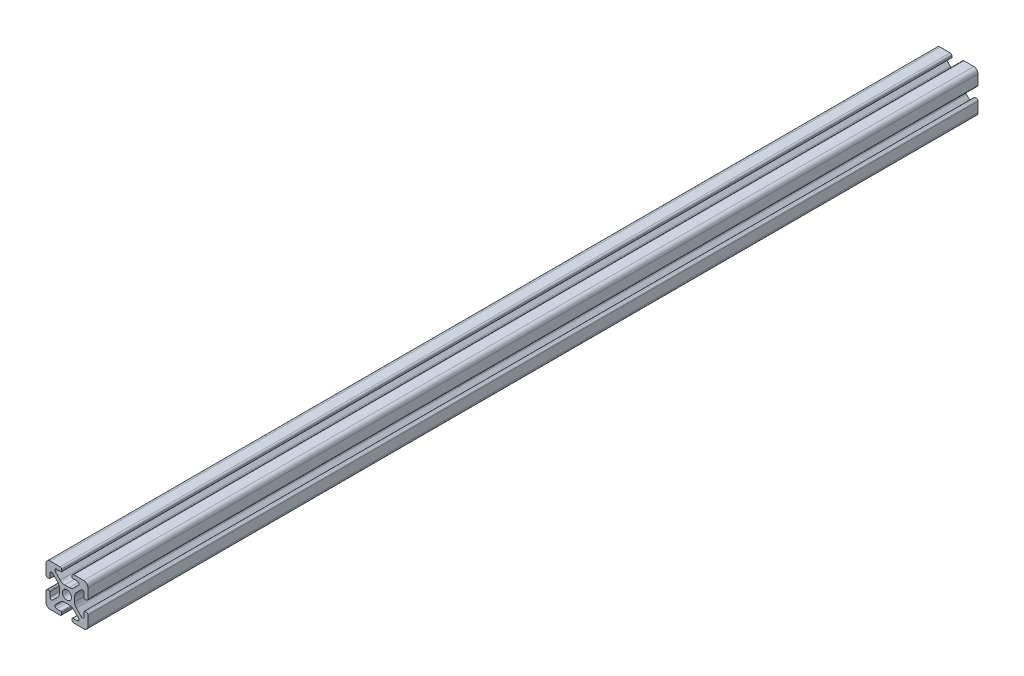
SolidWorks part; units mm, degrees
ref_plane "Front Plane" through (0, 0, 0) normal (0, 0, 1) x (1, 0, 0)
ref_plane "Top Plane" through (0, 0, 0) normal (0, 1, 0) x (1, 0, 0)
ref_plane "Right Plane" through (0, 0, 0) normal (1, 0, 0) x (0, 0, -1)
sketch "Sketch1" plane through (0, 0, 0) normal (0, 0, 1) x (1, 0, 0)
  line L0 (0, 10) -> (0, -10) construction
  line L1 (10, 0) -> (-10, 0) construction
  line L2 (-2.5, 10) -> (2.5, 10) construction
  line L3 (-5.75, 8.2) -> (5.75, 8.2) construction
  circle A0 centre (0, 0) radius 2.15 construction
  point P4 (0, 0)
  point P8 (0, 0)
  point P10 (0, 3.6)
  point P14 (0, 10)
  point P17 (0, 8.2)
  dimension "Thru Hole" = 4.3
  dimension "Height" = 20
  dimension "T Slot Depth" = 6.4
  dimension "T Slot Top Width" = 5
  dimension "T Slot Max Width" = 11.5
  dimension "Wall" = 1.8
sketch "Sketch2" plane through (0, 0, 0) normal (1, 0, 0) x (0, 0, -1)
  line L0 (212.5, 0) -> (-212.5, 0) construction
  point P4 (0, 0)
  dimension "D1" = 425
sketch "Sketch3" plane through (0, 0, 0) normal (0, 0, 1) x (1, 0, 0)
  line L0 (3.2874, 10) -> (8, 10)
  line L1 (10, 8) -> (10, -8) construction
  line L2 (8, -10) -> (-8, -10) construction
  line L3 (-10, 10) -> (10, -10) construction
  line L4 (2.5, 9.2126) -> (2.5, 8.5048)
  line L5 (-5.75, 8.2) -> (5.75, 8.2) construction
  line L6 (2.8048, 8.2) -> (4.9118, 8.2)
  line L7 (5.5045, 6.7691) -> (3.2141, 4.4787)
  line L8 (1.0928, 3.6) -> (-1.0928, 3.6)
  line L9 (0, 10) -> (0, -10) construction
  line L10 (5.75, 8.2) -> (5.75, 0) construction
  line L11 (10, 0) -> (-10, 0) construction
  line L12 (0, 0) -> (0, 10) construction
  line L13 (-2.5, 9.2126) -> (-2.5, 8.5048)
  line L14 (-5.5045, 6.7691) -> (-3.2141, 4.4787)
  line L15 (-2.8048, 8.2) -> (-4.9118, 8.2)
  line L16 (-3.2874, 10) -> (-8, 10)
  line L17 (0, 0) -> (-10, 0) construction
  line L18 (-10, 3.2874) -> (-10, 8)
  line L19 (-8.2, 2.8048) -> (-8.2, 4.9118)
  line L20 (-6.7691, 5.5045) -> (-4.4787, 3.2141)
  line L21 (-9.2126, 2.5) -> (-8.5048, 2.5)
  line L22 (-3.6, -1.0928) -> (-3.6, 1.0928)
  line L23 (-6.7691, -5.5045) -> (-4.4787, -3.2141)
  line L24 (-8.2, -2.8048) -> (-8.2, -4.9118)
  line L25 (-9.2126, -2.5) -> (-8.5048, -2.5)
  line L26 (-10, -3.2874) -> (-10, -8)
  line L27 (9.2126, -2.5) -> (8.5048, -2.5)
  line L28 (8.2, -2.8048) -> (8.2, -4.9118)
  line L29 (6.7691, -5.5045) -> (4.4787, -3.2141)
  line L30 (3.6, -1.0928) -> (3.6, 1.0928)
  line L31 (9.2126, 2.5) -> (8.5048, 2.5)
  line L32 (6.7691, 5.5045) -> (4.4787, 3.2141)
  line L33 (8.2, 2.8048) -> (8.2, 4.9118)
  line L34 (10, 8) -> (10, 3.2874)
  line L35 (10, -3.2874) -> (10, -8)
  line L36 (3.2874, -10) -> (8, -10)
  line L37 (-3.2874, -10) -> (-8, -10)
  line L38 (-6.7691, -5.5045) -> (-4.4787, -3.2141)
  line L39 (-2.8048, -8.2) -> (-4.9118, -8.2)
  line L40 (-5.5045, -6.7691) -> (-3.2141, -4.4787)
  line L41 (-2.5, -9.2126) -> (-2.5, -8.5048)
  line L42 (1.0928, -3.6) -> (-1.0928, -3.6)
  line L43 (5.5045, -6.7691) -> (3.2141, -4.4787)
  line L44 (2.8048, -8.2) -> (4.9118, -8.2)
  line L45 (2.5, -9.2126) -> (2.5, -8.5048)
  arc A0 (4.9118, 8.2) -> (5.5045, 6.7691) centre (4.9118, 7.3618) cw
  arc A1 (3.2141, 4.4787) -> (1.0928, 3.6) centre (1.0928, 6.6) cw
  circle A2 centre (0, 0) radius 2.15 construction
  circle A3 centre (0, 0) radius 2.15
  arc A4 (3.2874, 10) -> (2.5, 9.2126) centre (3.2874, 9.2126) ccw
  arc A5 (2.5, 8.5048) -> (2.8048, 8.2) centre (2.8048, 8.5048) ccw
  arc A6 (-3.2874, 10) -> (-2.5, 9.2126) centre (-3.2874, 9.2126) cw
  arc A7 (-4.9118, 8.2) -> (-5.5045, 6.7691) centre (-4.9118, 7.3618) ccw
  arc A8 (-3.2141, 4.4787) -> (-1.0928, 3.6) centre (-1.0928, 6.6) ccw
  arc A9 (-2.5, 8.5048) -> (-2.8048, 8.2) centre (-2.8048, 8.5048) cw
  arc A10 (-8.5048, 2.5) -> (-8.2, 2.8048) centre (-8.5048, 2.8048) ccw
  arc A11 (-4.4787, 3.2141) -> (-3.6, 1.0928) centre (-6.6, 1.0928) cw
  arc A12 (-8.2, 4.9118) -> (-6.7691, 5.5045) centre (-7.3618, 4.9118) cw
  arc A13 (-10, 3.2874) -> (-9.2126, 2.5) centre (-9.2126, 3.2874) ccw
  arc A14 (-8.5048, -2.5) -> (-8.2, -2.8048) centre (-8.5048, -2.8048) cw
  arc A15 (-10, -3.2874) -> (-9.2126, -2.5) centre (-9.2126, -3.2874) cw
  arc A16 (-4.4787, -3.2141) -> (-3.6, -1.0928) centre (-6.6, -1.0928) ccw
  arc A17 (-8.2, -4.9118) -> (-6.7691, -5.5045) centre (-7.3618, -4.9118) ccw
  arc A26 (-8, -10) -> (-10, -8) centre (-8, -8) cw
  arc A27 (-8, 10) -> (-10, 8) centre (-8, 8) ccw
  arc A28 (8, 10) -> (10, 8) centre (8, 8) cw
  arc A29 (10, -8) -> (8, -10) centre (8, -8) cw
  arc A30 (8.2, -4.9118) -> (6.7691, -5.5045) centre (7.3618, -4.9118) cw
  arc A31 (4.4787, -3.2141) -> (3.6, -1.0928) centre (6.6, -1.0928) cw
  arc A32 (10, -3.2874) -> (9.2126, -2.5) centre (9.2126, -3.2874) ccw
  arc A33 (8.5048, -2.5) -> (8.2, -2.8048) centre (8.5048, -2.8048) ccw
  arc A34 (10, 3.2874) -> (9.2126, 2.5) centre (9.2126, 3.2874) cw
  arc A35 (8.2, 4.9118) -> (6.7691, 5.5045) centre (7.3618, 4.9118) ccw
  arc A36 (4.4787, 3.2141) -> (3.6, 1.0928) centre (6.6, 1.0928) ccw
  arc A37 (8.5048, 2.5) -> (8.2, 2.8048) centre (8.5048, 2.8048) cw
  arc A38 (-2.5, -8.5048) -> (-2.8048, -8.2) centre (-2.8048, -8.5048) ccw
  arc A39 (-3.2141, -4.4787) -> (-1.0928, -3.6) centre (-1.0928, -6.6) cw
  arc A40 (-4.9118, -8.2) -> (-5.5045, -6.7691) centre (-4.9118, -7.3618) cw
  arc A41 (-3.2874, -10) -> (-2.5, -9.2126) centre (-3.2874, -9.2126) ccw
  arc A42 (2.5, -8.5048) -> (2.8048, -8.2) centre (2.8048, -8.5048) cw
  arc A43 (3.2874, -10) -> (2.5, -9.2126) centre (3.2874, -9.2126) cw
  arc A44 (3.2141, -4.4787) -> (1.0928, -3.6) centre (1.0928, -6.6) ccw
  arc A45 (4.9118, -8.2) -> (5.5045, -6.7691) centre (4.9118, -7.3618) ccw
  point P36 (2.5, 10)
  point P39 (2.5, 8.2)
  point P49 (0, 3.6)
  point P77 (-3.6, 0)
  point P78 (-8.2, -2.5)
  point P79 (-10, -2.5)
  point P104 (-10, -10)
  point P110 (10, 10)
  point P114 (10, -2.5)
  point P115 (8.2, -2.5)
  point P116 (3.6, 0)
  point P141 (0, -3.6)
  dimension "D1" = 3
  dimension "D2" = 0.8382
  dimension "D4" = 0.7874
  dimension "D5" = 0.3048
  dimension "D6" = 2
  dimension "D3" = 45
extrude "Boss-Extrude1" add sketch "Sketch3" along normal up to vertex (212.5 mm away) and the other way up to vertex (212.5 mm away) contours A45 L44 A42 L45 A43 L36 A29 L35 A32 L27 A33 L28 A30 L29 A31 L30 A36 L32 A35 L33 A37 L31 A34 L34 A28 L0 A4 L4 A5 L6 A0 L7 A1 L8 A8 L14 A7 L15 A9 L13 A6 L16 A27 L18 A13 L21 A10 L19 A12 L20 A11 up to point (0, 0, 212.5) other way up to point (0, 0, -212.5)
